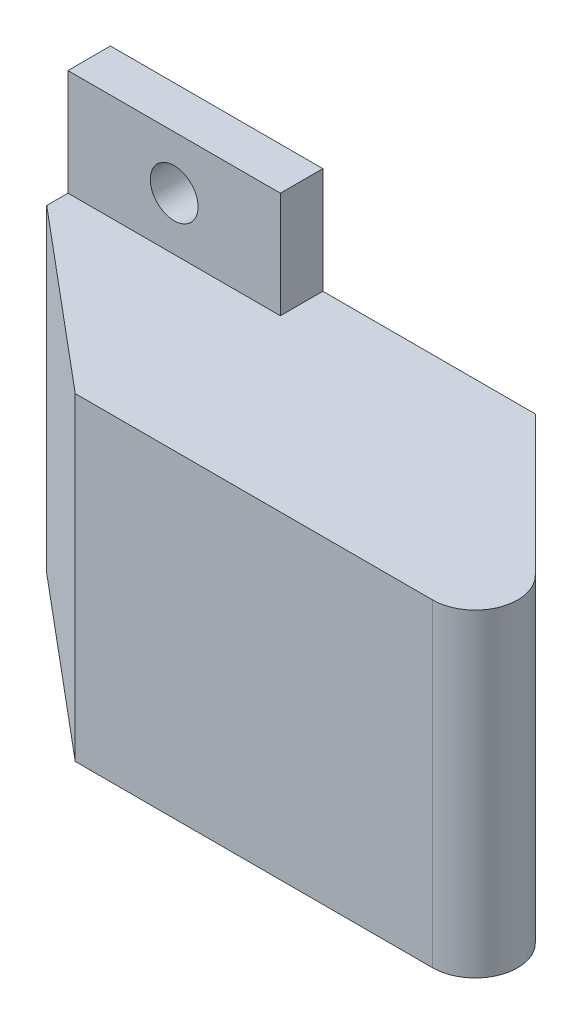
SolidWorks part; units mm, degrees
ref_plane "Front Plane" through (0, 0, 0) normal (0, 0, 1) x (1, 0, 0)
ref_plane "Top Plane" through (0, 0, 0) normal (0, 1, 0) x (1, 0, 0)
ref_plane "Right Plane" through (0, 0, 0) normal (1, 0, 0) x (0, 0, -1)
sketch "Sketch1" plane through (0, 0, 0) normal (1, 0, 0) x (0, 0, -1)
  line L1 (0, 0) -> (20, 0)
  line L2 (0, 0) -> (0, 30)
  line L3 (0, 30) -> (20, 30)
  line L4 (20, 0) -> (20, 30)
  dimension "D1" = 20
  dimension "D2" = 30
extrude "Boss-Extrude1" add sketch "Sketch1" along normal blind 60
sketch "Sketch2" plane through (0, 0, -20) normal (0, 0, -1) x (-1, 0, 0)
  line L0 (-60, 30) -> (0, 30) construction
  line L1 (0, 40) -> (-20, 40)
  line L2 (0, 40) -> (0, -10)
  line L3 (0, -10) -> (-20, -10)
  line L4 (-20, 40) -> (-20, -10)
  line L5 (-60, 0) -> (0, 0) construction
  line L6 (0, 0) -> (0, 30) construction
  circle A0 centre (-10, 35) radius 2.25
  circle A1 centre (-10, -5) radius 2.25
  dimension "D4" = 4.5
  dimension "D5" = 4.5
  dimension "D6" = 5
  dimension "D7" = 5
  dimension "D1" = 20
  dimension "D2" = 10
  dimension "D3" = 10
extrude "Boss-Extrude2" add sketch "Sketch2" against normal blind 4
sketch "Sketch3" plane through (0, 30, 0) normal (0, 1, 0) x (1, 0, 0)
  line L0 (60, 20) -> (40, 20)
  line L1 (60, 20) -> (20, 20) construction
  line L2 (40, 20) -> (60, 0)
  line L3 (60, 20) -> (60, 0) construction
  line L4 (60, 0) -> (60, 20)
  line L5 (0, 16) -> (0, 20) construction
  dimension "D1" = 45
  dimension "D2" = 40
extrude "Cut-Extrude1" cut sketch "Sketch3" against normal through all
fillet "Fillet1" radius 4 1 edges at (60, 15, 0)
sketch "Sketch4" plane through (30, 0, -30) normal (0.7071, 0, -0.7071) x (-0.7071, 0, -0.7071)
  line L0 (-14.1421, 0) -> (-14.1421, 30) construction
  line L1 (-21.1421, 25) -> (-31.1421, 25)
  line L2 (-21.1421, 25) -> (-21.1421, 5)
  line L3 (-21.1421, 5) -> (-31.1421, 5)
  line L4 (-31.1421, 25) -> (-31.1421, 5)
  point P6 (-21.1421, 15)
  point P7 (-14.1421, 15)
  dimension "D1" = 7
  dimension "D2" = 10
  dimension "D3" = 20
extrude "Cut-Extrude2" cut sketch "Sketch4" against normal blind 5
chamfer "Chamfer1" distance 14 angle 50 1 edges at (0, 15, 0)
